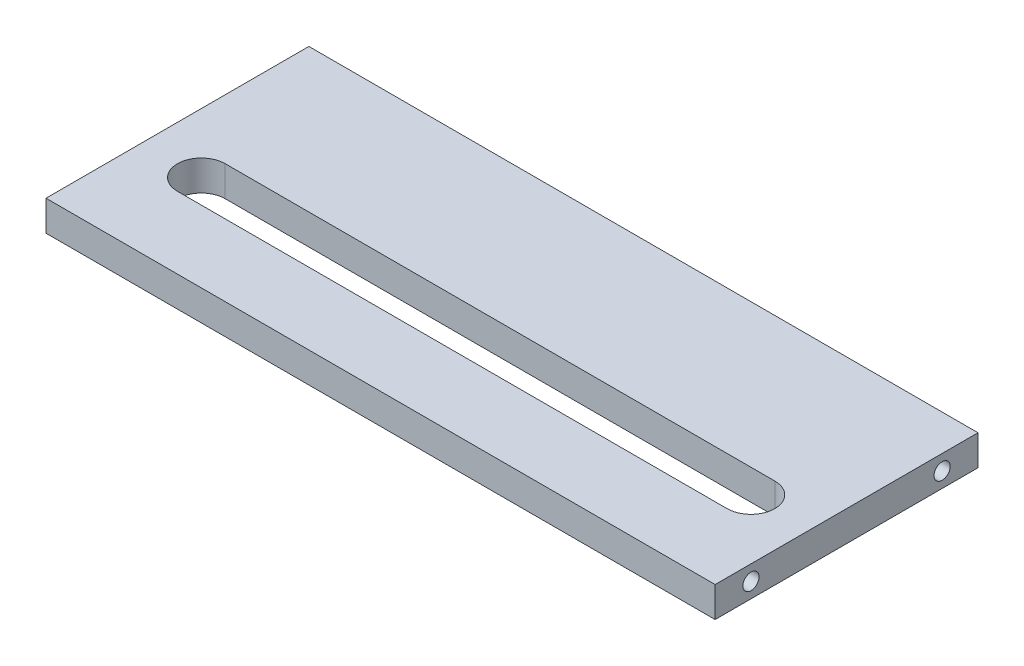
SolidWorks part; units mm, degrees
ref_plane "Alzado" through (0, 0, 0) normal (0, 0, 1) x (1, 0, 0)
ref_plane "Planta" through (0, 0, 0) normal (0, 1, 0) x (1, 0, 0)
ref_plane "Vista lateral" through (0, 0, 0) normal (1, 0, 0) x (0, 0, -1)
sketch "Croquis1" plane through (0, 0, 0) normal (0, 1, 0) x (1, 0, 0)
  line L1 (-125.7057, 56.7568) -> (154.2943, 56.7568)
  line L2 (-125.7057, 56.7568) -> (-125.7057, -53.2432)
  line L3 (-125.7057, -53.2432) -> (154.2943, -53.2432)
  line L4 (154.2943, 56.7568) -> (154.2943, -53.2432)
  dimension "D1" = 280
  dimension "D2" = 110
extrude "Saliente-Extruir1" add sketch "Croquis1" along normal blind 12.7
sketch "Croquis2" plane through (0, 0, 0) normal (0, 1, 0) x (1, 0, 0)
  line L0 (154.2943, 56.7568) -> (-125.7057, 56.7568) construction
  line L1 (-100.7057, -3.2432) -> (129.2943, -3.2432)
  line L2 (154.2943, -53.2432) -> (154.2943, 56.7568) construction
  line L3 (-100.7057, -23.2432) -> (129.2943, -23.2432)
  arc A0 (129.2943, -23.2432) -> (129.2943, -3.2432) centre (129.2943, -13.2432) ccw
  arc A1 (-100.7057, -3.2432) -> (-100.7057, -23.2432) centre (-100.7057, -13.2432) ccw
  dimension "D4" = 25
  dimension "D1" = 60
  dimension "D2" = 20
  dimension "D3" = 230
extrude "Cortar-Extruir2" cut sketch "Croquis2" along normal blind 20
sketch "Croquis5" plane through (-125.7057, 0, 0) normal (-1, 0, 0) x (0, 0, 1)
  line L0 (53.2432, 12.7) -> (53.2432, 0) construction
  line L1 (-56.7568, 0) -> (53.2432, 0) construction
  line L2 (-56.7568, 12.7) -> (-56.7568, 0) construction
  line L3 (-56.7568, 12.7) -> (53.2432, 12.7) construction
  circle A0 centre (38.2432, 6.35) radius 3.375
  circle A1 centre (-41.7568, 6.35) radius 3.375
  dimension "D3" = 6.75
  dimension "D6" = 6.75
  dimension "D1" = 15
  dimension "D2" = 6.35
  dimension "D4" = 15
  dimension "D5" = 6.35
extrude "Cortar-Extruir5" cut sketch "Croquis5" against normal blind 30
sketch "Croquis6" plane through (154.2943, 0, 0) normal (1, 0, 0) x (0, 0, -1)
  line L0 (-53.2432, 12.7) -> (56.7568, 12.7) construction
  line L1 (-53.2432, 12.7) -> (-53.2432, 0) construction
  line L2 (56.7568, 12.7) -> (56.7568, 0) construction
  circle A0 centre (41.7568, 6.35) radius 3.375
  circle A1 centre (-38.2432, 6.35) radius 3.375
  dimension "D1" = 6.75
  dimension "D2" = 6.75
  dimension "D3" = 6.35
  dimension "D4" = 6.35
  dimension "D5" = 15
  dimension "D6" = 15
extrude "Cortar-Extruir6" cut sketch "Croquis6" against normal blind 30
